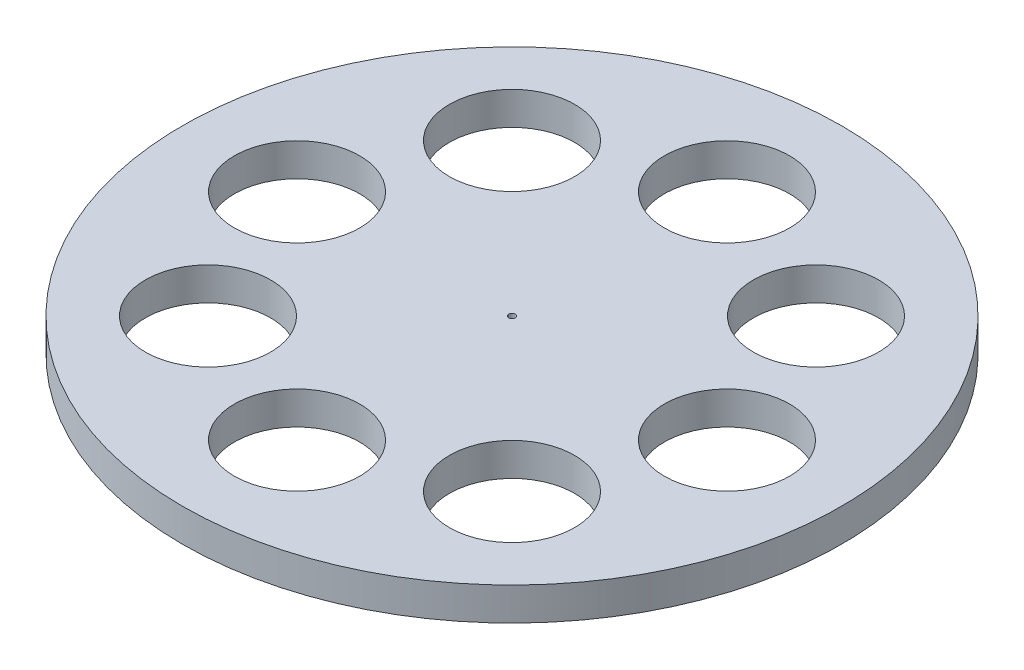
SolidWorks part; units mm, degrees
ref_plane "Front Plane" through (0, 0, 0) normal (0, 0, 1) x (1, 0, 0)
ref_plane "Top Plane" through (0, 0, 0) normal (0, 1, 0) x (1, 0, 0)
ref_plane "Right Plane" through (0, 0, 0) normal (1, 0, 0) x (0, 0, -1)
sketch "Sketch1" plane through (0, 0, 0) normal (0, 1, 0) x (1, 0, 0)
  circle A0 centre (0, 0) radius 50
extrude "Boss-Extrude1" add sketch "Sketch1" along normal blind 5
sketch "Sketch2" plane through (0, 5, 0) normal (0, 1, 0) x (1, 0, 0)
  circle A0 centre (0, 32.6142) radius 9.5
  circle A1 centre (0, 0) radius 0.5
  circle A2 centre (23.0617, 23.0617) radius 9.5
  circle A3 centre (32.6142, 0) radius 9.5
  circle A4 centre (23.0617, -23.0617) radius 9.5
  circle A5 centre (0, -32.6142) radius 9.5
  circle A6 centre (-23.0617, -23.0617) radius 9.5
  circle A7 centre (-32.6142, 0) radius 9.5
  circle A8 centre (-23.0617, 23.0617) radius 9.5
  point P5 (0, 32.6142)
  point P22 (0, 0)
  dimension "D1" = 8
extrude "Cut-Extrude1" cut sketch "Sketch2" against normal blind 5
